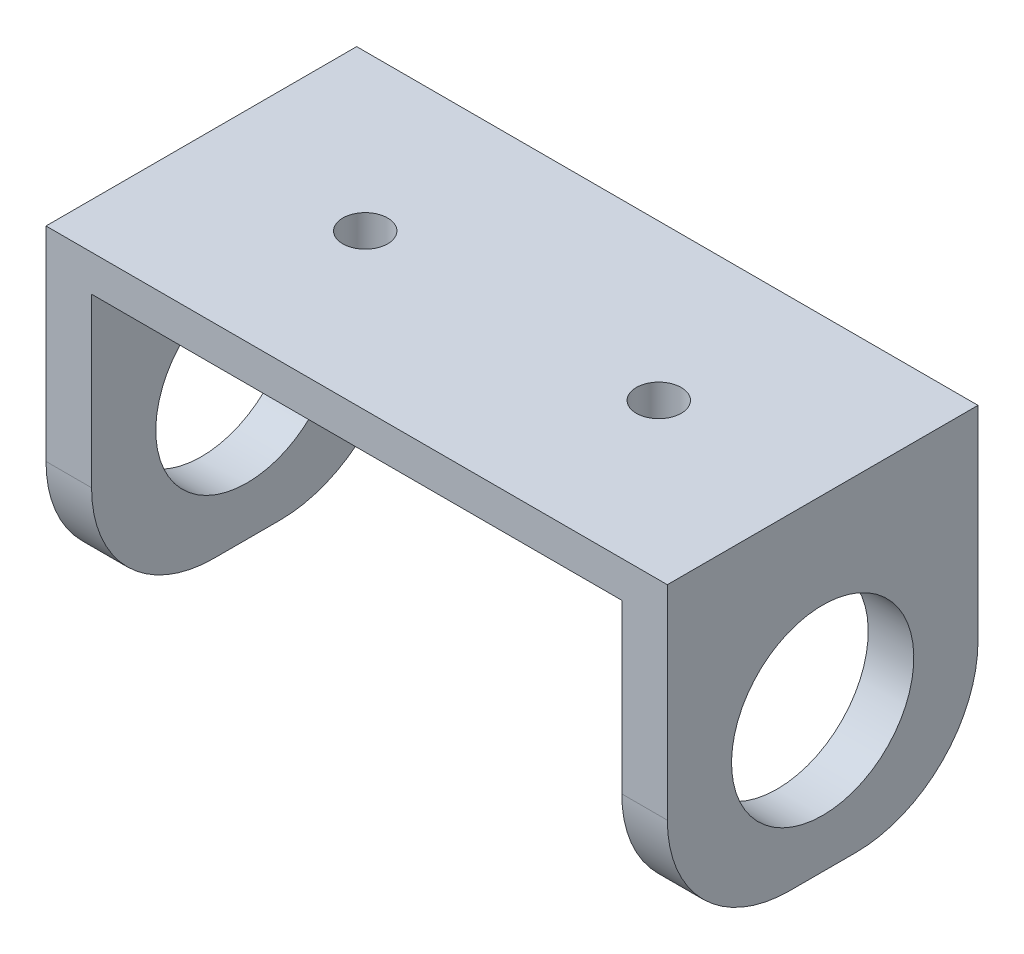
SolidWorks part; units mm, degrees
material "PE Low/Medium Density"
ref_plane "Front Plane" through (0, 0, 0) normal (0, 0, 1) x (1, 0, 0)
ref_plane "Top Plane" through (0, 0, 0) normal (0, 1, 0) x (1, 0, 0)
ref_plane "Right Plane" through (0, 0, 0) normal (1, 0, 0) x (0, 0, -1)
sketch "Sketch1" plane through (0, 0, 0) normal (0, 0, 1) x (1, 0, 0)
  line L0 (-76.7177, 44.0383) -> (-0.5177, 44.0383)
  line L1 (-76.7177, 44.0383) -> (-76.7177, 4.0283)
  line L2 (-76.7177, 4.0283) -> (-71.1297, 4.0283)
  line L3 (-71.1297, 4.0283) -> (-71.1297, 39.5883)
  line L4 (-71.1297, 39.5883) -> (-6.1057, 39.5883)
  line L5 (-6.1057, 39.5883) -> (-6.1057, 4.0283)
  line L6 (-6.1057, 4.0283) -> (-0.5177, 4.0283)
  line L7 (-0.5177, 44.0383) -> (-0.5177, 4.0283)
extrude "Boss-Extrude1" add sketch "Sketch1" along normal blind 38.1
ref_plane "Plane1" through (-38.6177, 0, 0) normal (-1, 0, 0) x (0, 0, 1)
sketch "Sketch5" plane through (-6.1057, 0, 0) normal (-1, 0, 0) x (0, 0, 1)
  circle A0 centre (19.05, 21.1783) radius 11.176
extrude "Cut-Extrude1" cut sketch "Sketch5" against normal blind 38.1
mirror "Mirror3" about plane through (-38.6177, 0, 0) normal (-1, 0, 0) of "Cut-Extrude1"
fillet "Fillet1" radius 15 4 edges at (-73.9237, 4.0283, 38.1) (-73.9237, 4.0283, 0) (-3.3117, 4.0283, 0) (-3.3117, 4.0283, 38.1)
sketch "Sketch6" plane through (0, 44.0383, 0) normal (0, 1, 0) x (1, 0, 0)
  circle A0 centre (-56.6177, -19.05) radius 1.51
  circle A1 centre (-20.6177, -19.05) radius 1.51
extrude "Cut-Extrude2" cut sketch "Sketch6" against normal blind 10
sketch "Sketch11" plane through (0, 44.0383, 0) normal (0, 1, 0) x (1, 0, 0)
  circle A0 centre (-56.6177, -19.05) radius 2.75
  circle A1 centre (-20.6177, -19.05) radius 2.75
extrude "Cut-Extrude5" cut sketch "Sketch11" against normal blind 5 contours A0 | A1
sketch "Sketch12" plane through (0, 0, 0) normal (0, 0, -1) x (-1, 0, 0)
  line L0 (6.1057, 39.5883) -> (71.1297, 39.5883)
  line L1 (71.1297, 39.5883) -> (6.1057, 39.5883) construction
  line L2 (65.0097, 39.5883) -> (65.0097, 33.6383) construction
  line L3 (6.1057, 39.5883) -> (6.1057, 28.6285)
  line L4 (11.9857, 39.5883) -> (11.9857, 33.6383) construction
  line L5 (71.1297, 39.5883) -> (71.1297, 28.6285)
  line L6 (19.0457, 33.6383) -> (57.9497, 33.6383)
  line L8 (6.1057, 39.5883) -> (6.1057, 19.0283) construction
  line L10 (6.1057, 28.6285) -> (11.9759, 28.6285)
  line L14 (71.1297, 19.0283) -> (71.1297, 39.5883) construction
  line L16 (65.2594, 28.6285) -> (71.1297, 28.6285)
  line L19 (71.1297, 39.5883) -> (6.1057, 39.5883) construction
  circle A0 centre (65.0097, 33.6383) radius 2.75
  circle A1 centre (11.9857, 33.6383) radius 2.75
  arc A2 (11.9759, 28.6285) -> (16.9857, 31.5783) centre (11.9759, 34.3576) ccw
  arc A3 (65.2594, 28.6285) -> (60.2497, 31.5783) centre (65.2594, 34.3576) cw
  arc A4 (16.9857, 31.5783) -> (19.0457, 33.6383) centre (19.0457, 31.5783) cw
  arc A5 (60.2497, 31.5783) -> (57.9497, 33.6383) centre (58.1897, 31.5923) ccw
  dimension "D1" = 5.7291
  dimension "D2" = 2.06
  dimension "D5" = 5.5
  dimension "D6" = 5.95
  dimension "D7" = 53.024
  dimension "D13" = 5.7291
  dimension "D14" = 2.06
  dimension "D3" = 38.904
  dimension "D4" = 5.8702
  dimension "D8" = 6.12
  dimension "D9" = 5.95
  dimension "D10" = 5.95
  dimension "D11" = 10.9598
  dimension "D12" = 10.9598
  dimension "D15" = 10.88
  dimension "D16" = 10.88
extrude "Boss-Extrude2" add sketch "Sketch12" against normal blind 3
sketch "Sketch13" plane through (0, 0, 3) normal (0, 0, 1) x (1, 0, 0)
  line L0 (-38.4977, 33.6383) -> (-38.4977, 39.5883) construction
  line L1 (-19.0457, 33.6383) -> (-57.9497, 33.6383) construction
  line L2 (-71.1297, 39.5883) -> (-6.1057, 39.5883) construction
  line L3 (-48.4977, 36.6133) -> (-28.4977, 36.6133) construction
  circle A0 centre (-28.4977, 36.6133) radius 1.5
  circle A1 centre (-48.4977, 36.6133) radius 1.5
  point P9 (-38.4977, 36.6133)
  dimension "D1" = 3
  dimension "D2" = 3
  dimension "D3" = 10
extrude "Cut-Extrude6" cut sketch "Sketch13" against normal blind 3
